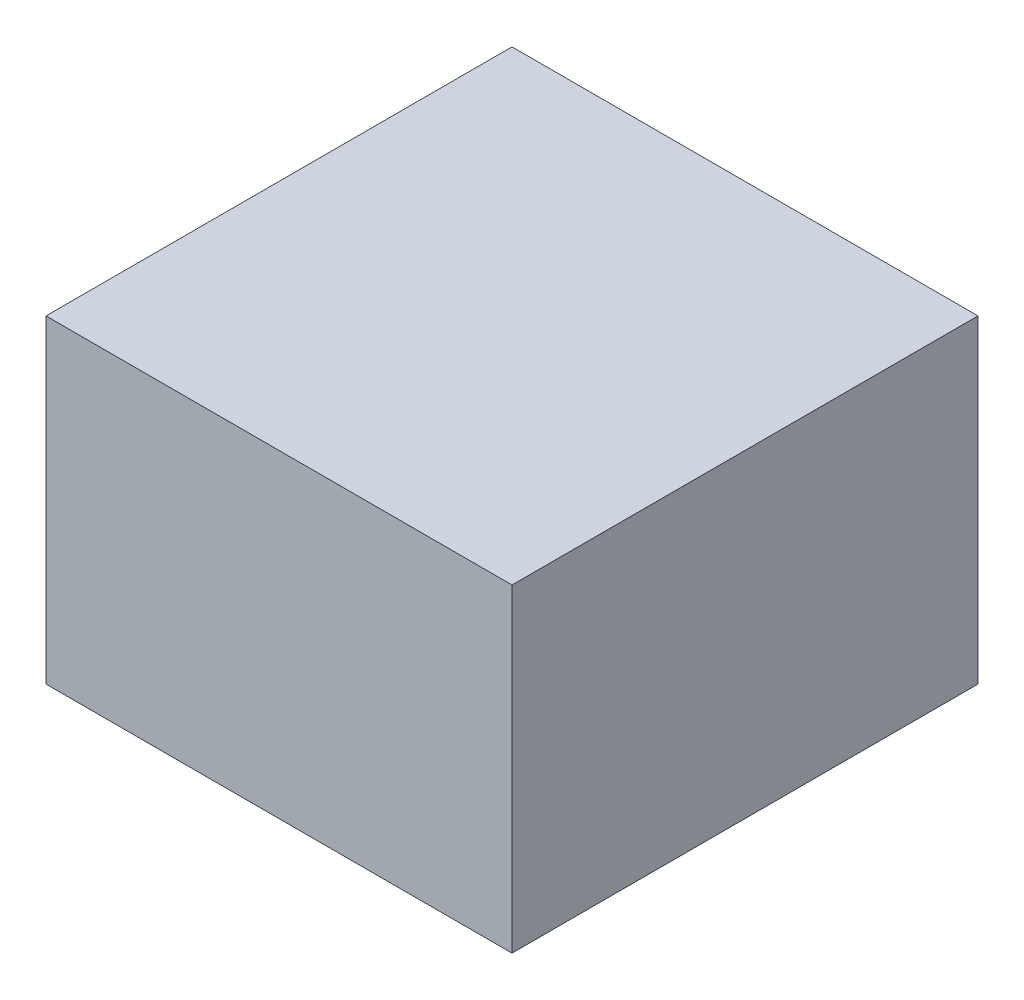
SolidWorks part; units mm, degrees
ref_plane "Front Plane" through (0, 0, 0) normal (0, 0, 1) x (1, 0, 0)
ref_plane "Top Plane" through (0, 0, 0) normal (0, 1, 0) x (1, 0, 0)
ref_plane "Right Plane" through (0, 0, 0) normal (1, 0, 0) x (0, 0, -1)
sketch "Sketch2" plane through (0, 0, 0) normal (0, 1, 0) x (1, 0, 0)
  line L1 (-57.6554, 150) -> (132.3446, 150)
  line L2 (-57.6554, 150) -> (-57.6554, -40)
  line L3 (-57.6554, -40) -> (132.3446, -40)
  line L4 (132.3446, 150) -> (132.3446, -40)
  line L5 (-57.6554, 150) -> (132.3446, -40) construction
  line L6 (-57.6554, -40) -> (132.3446, 150) construction
  point P0 (37.3446, 55)
  dimension "D1" = 190
  dimension "D2" = 190
extrude "Boss-Extrude1" add sketch "Sketch2" along normal blind 130
sketch "Sketch3" plane through (-57.6554, 0, 0) normal (-1, 0, 0) x (0, 0, 1)
  line L0 (-150, 130) -> (-150, 0) construction
  line L1 (30, 10) -> (-140, 10)
  line L2 (30, 10) -> (30, 120)
  line L3 (30, 120) -> (-140, 120)
  line L4 (-140, 10) -> (-140, 120)
  line L5 (-150, 0) -> (40, 0) construction
  dimension "D1" = 170
  dimension "D2" = 10
  dimension "D3" = 110
  dimension "D4" = 10
extrude "Boss-Extrude2" add sketch "Sketch3" along normal blind 2
sketch "Sketch4" plane through (-59.6554, 0, 0) normal (-1, 0, 0) x (0, 0, 1)
  line L0 (-150, 0) -> (40, 0) construction
  line L1 (-150, 130) -> (40, 130) construction
  line L2 (40, 130) -> (40, 0) construction
  circle A0 centre (-25, 25) radius 4
  circle A1 centre (-45, 25) radius 4
  circle A2 centre (-25, 105) radius 4
  circle A3 centre (-65, 25) radius 4
  circle A4 centre (-85, 25) radius 4
  circle A5 centre (-45, 105) radius 4
  circle A6 centre (-65, 105) radius 4
  circle A7 centre (-85, 105) radius 4
  dimension "D1" = 8
  dimension "D2" = 8
  dimension "D3" = 8
  dimension "D4" = 8
  dimension "D5" = 8
  dimension "D6" = 8
  dimension "D7" = 20
  dimension "D8" = 20
  dimension "D9" = 20
  dimension "D10" = 20
  dimension "D11" = 20
  dimension "D12" = 20
  dimension "D13" = 25
  dimension "D14" = 25
  dimension "D15" = 65
  dimension "D16" = 65
extrude "Boss-Extrude3" add sketch "Sketch4" along normal blind 8
